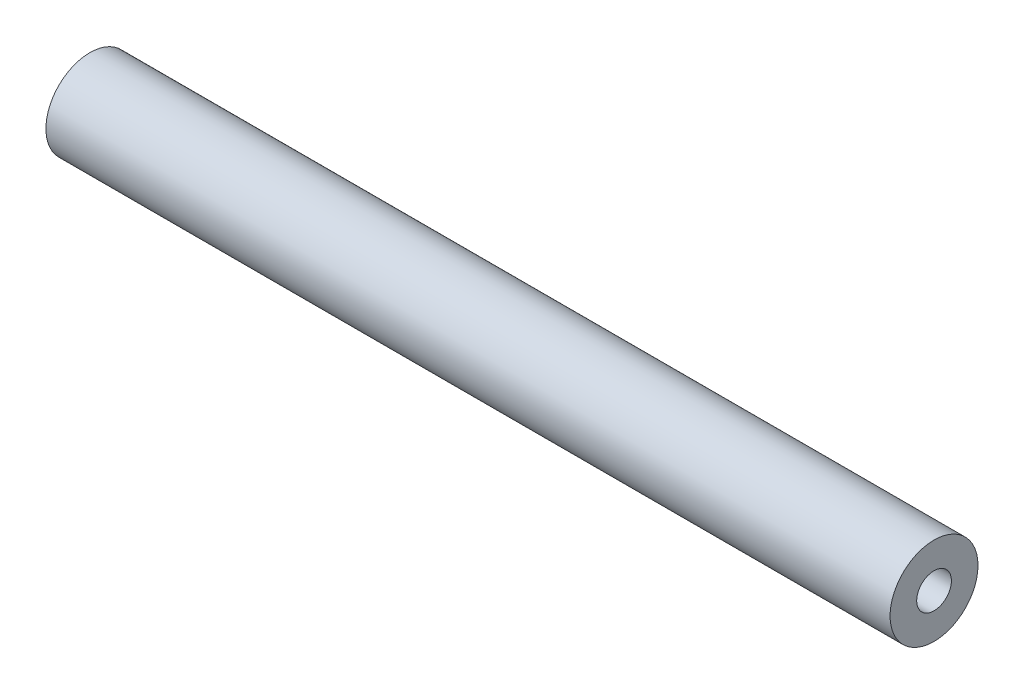
SolidWorks part; units mm, degrees
ref_plane "Front Plane" through (0, 0, 0) normal (0, 0, 1) x (1, 0, 0)
ref_plane "Top Plane" through (0, 0, 0) normal (0, 1, 0) x (1, 0, 0)
ref_plane "Right Plane" through (0, 0, 0) normal (1, 0, 0) x (0, 0, -1)
sketch "Sketch1" plane through (0, 0, 0) normal (1, 0, 0) x (0, 0, -1)
  circle A0 centre (0, 0) radius 24.13
  circle A1 centre (0, 0) radius 9.525
  dimension "D1" = 48.26
  dimension "D2" = 19.05
extrude "Boss-Extrude1" add sketch "Sketch1" along normal mid plane 463.423
